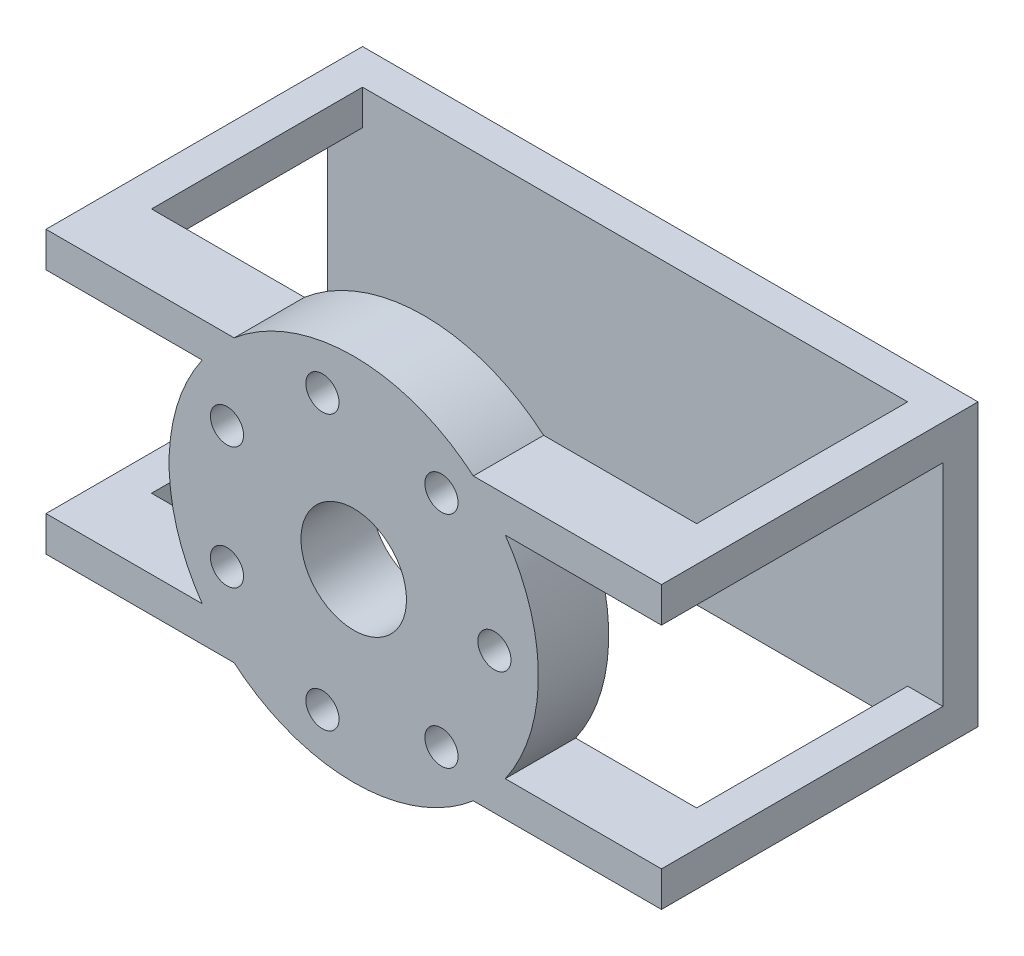
SolidWorks part; units mm, degrees
ref_plane "Front Plane" through (0, 0, 0) normal (0, 0, 1) x (1, 0, 0)
ref_plane "Top Plane" through (0, 0, 0) normal (0, 1, 0) x (1, 0, 0)
ref_plane "Right Plane" through (0, 0, 0) normal (1, 0, 0) x (0, 0, -1)
sketch "Sketch1" plane through (0, 0, 0) normal (0, 1, 0) x (1, 0, 0)
  line L1 (-87.5, 45) -> (87.5, 45)
  line L2 (-87.5, 45) -> (-87.5, -45)
  line L3 (-87.5, -45) -> (87.5, -45)
  line L4 (87.5, 45) -> (87.5, -45)
  line L5 (-87.5, 45) -> (87.5, -45) construction
  line L6 (-87.5, -45) -> (87.5, 45) construction
  point P0 (0, 0)
  dimension "D1" = 175
  dimension "D2" = 90
extrude "Boss-Extrude1" add sketch "Sketch1" along normal blind 80
sketch "Sketch2" plane through (0, 80, 0) normal (0, 1, 0) x (1, 0, 0)
  line L0 (87.5, 45) -> (-87.5, 45) construction
  line L1 (-77.5, 35) -> (77.5, 35)
  line L2 (-77.5, 35) -> (-77.5, -25)
  line L3 (-77.5, -25) -> (77.5, -25)
  line L4 (77.5, 35) -> (77.5, -25)
  line L5 (-87.5, 45) -> (-87.5, -45) construction
  line L6 (87.5, -45) -> (87.5, 45) construction
  line L7 (-87.5, -45) -> (87.5, -45) construction
  dimension "D1" = 10
  dimension "D2" = 10
  dimension "D3" = 10
  dimension "D4" = 20
extrude "Cut-Extrude1" cut sketch "Sketch2" against normal blind 80
sketch "Sketch3" plane through (87.5, 0, 0) normal (1, 0, 0) x (0, 0, -1)
  line L0 (45, 80) -> (45, 0) construction
  line L1 (-25, 70) -> (35, 70)
  line L2 (-25, 70) -> (-25, 10)
  line L3 (-25, 10) -> (35, 10)
  line L4 (35, 70) -> (35, 10)
  line L5 (-45, 80) -> (45, 80) construction
  line L6 (-45, 0) -> (45, 0) construction
  line L7 (-45, 80) -> (-45, 0) construction
  dimension "D1" = 10
  dimension "D2" = 10
  dimension "D3" = 10
  dimension "D4" = 20
extrude "Cut-Extrude2" cut sketch "Sketch3" against normal through all
sketch "Sketch4" plane through (0, 0, 45) normal (0, 0, 1) x (1, 0, 0)
  circle A0 centre (0, 40) radius 52.5
  dimension "D1" = 105
extrude "Boss-Extrude3" add sketch "Sketch4" against normal blind 20
sketch "Sketch5" plane through (0, 0, 45) normal (0, 0, 1) x (1, 0, 0)
  line L0 (87.5, 70) -> (43.0842, 70)
  line L1 (87.5, 80) -> (87.5, 0) construction
  line L2 (34.0037, 80) -> (87.5, 80) construction
  line L3 (43.0842, 10) -> (87.5, 10)
  line L4 (34.0037, 0) -> (87.5, 0) construction
  line L5 (-43.0842, 70) -> (-87.5, 70)
  line L6 (-87.5, 80) -> (-87.5, 0) construction
  line L7 (-43.0842, 10) -> (-87.5, 10)
  line L8 (-87.5, 80) -> (-34.0037, 80) construction
  line L9 (-87.5, 0) -> (-34.0037, 0) construction
  line L10 (-87.5, 70) -> (-87.5, 10)
  line L11 (87.5, 70) -> (87.5, 10)
  arc A0 (-43.0842, 70) -> (-43.0842, 10) centre (0, 40) ccw
  arc A1 (43.0842, 10) -> (43.0842, 70) centre (0, 40) ccw
  dimension "D1" = 105
  dimension "D2" = 10
  dimension "D3" = 10
  dimension "D4" = 10
  dimension "D5" = 10
extrude "Cut-Extrude3" cut sketch "Sketch5" against normal blind 20
sketch "Sketch6" plane through (0, 0, 45) normal (0, 0, 1) x (1, 0, 0)
  circle A0 centre (0, 40) radius 40 construction
  circle A1 centre (40, 40) radius 4.7152
  dimension "D1" = 80
  dimension "D2" = 9.4304
extrude "Cut-Extrude4" cut sketch "Sketch6" against normal blind 20
pattern_circular "CirPattern1" count 7 over 360 about axis through (0, 40, 0) along (0, 0, 1) of "Cut-Extrude4"
sketch "Sketch7" plane through (0, 0, 45) normal (0, 0, 1) x (1, 0, 0)
  circle A0 centre (0, 40) radius 15
  dimension "D1" = 30
extrude "Cut-Extrude5" cut sketch "Sketch7" against normal blind 20 contours A0
